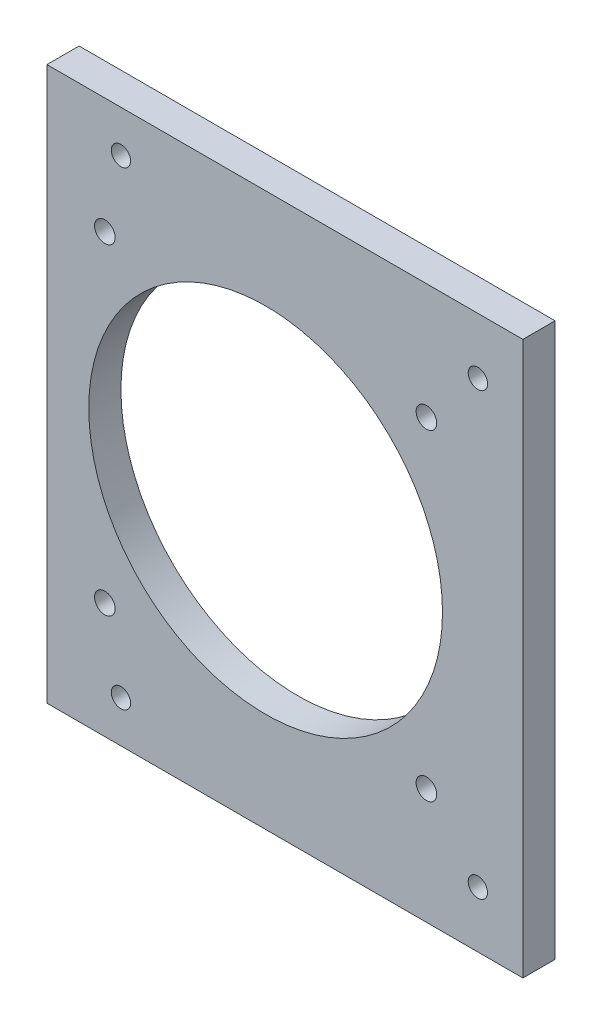
SolidWorks part; units mm, degrees
material "PBT Общее назначение"
ref_plane "Спереди" through (0, 0, 0) normal (0, 0, 1) x (1, 0, 0)
ref_plane "Сверху" through (0, 0, 0) normal (0, 1, 0) x (1, 0, 0)
ref_plane "Справа" through (0, 0, 0) normal (1, 0, 0) x (0, 0, -1)
sketch "Эскиз2" plane through (0, 0, 0) normal (0, 1, 0) x (1, 0, 0)
  line L0 (0, 0) -> (0, -131.0411) construction
  line L1 (0, 0) -> (-67.0136, 0) construction
sketch "Эскиз3" plane through (0, 0, 0) normal (0, 0, 1) x (1, 0, 0)
  line L0 (0, 0) -> (0, 105.2454) construction
sketch "Эскиз1" plane through (0, 0, 81) normal (0, 0, 1) x (1, 0, 0)
  line L0 (2.5, -5) -> (2.5, 95)
  line L1 (-67, -5) -> (-67, 95)
  line L2 (0, 0) -> (-67.0136, 0) construction
  line L3 (0, 0) -> (0, 105.2454) construction
  line L4 (-4.5, 79.25) -> (-4.5, 10.75) construction
  line L9 (2.5, 95) -> (-67, 95)
  line L11 (-67, -5) -> (2.5, -5)
  circle A1 centre (-60, 8.5) radius 1.5
  circle A6 centre (-60, 81.5) radius 1.5
  circle A8 centre (-4.5, 79.25) radius 1.5
  circle A10 centre (-4.5, 10.75) radius 1.5
  dimension "D5" = 7
  dimension "D6" = 7
  dimension "D3" = 3
  dimension "D4" = 13.5
  dimension "D7" = 15.75
  dimension "D8" = 15.75
  dimension "D9" = 7
  dimension "D10" = 13.5
  dimension "D2" = 100
  dimension "D1" = 69.5
  dimension "D11" = 5
  dimension "D12" = 2.5
extrude "Бобышка-Вытянуть1" add sketch "Эскиз1" against normal blind 5
sketch "Эскиз4" plane through (-67, 0, 0) normal (-1, 0, 0) x (0, 0, 1)
  line L0 (76, 95) -> (76, -5) construction
  line L1 (76, 95) -> (66, 95) construction
  line L2 (76, -5) -> (66, -5) construction
  line L3 (66, 95) -> (66, -5) construction
  dimension "D1" = 10
sketch "Эскиз5" plane through (0, 0, 81) normal (0, 0, 1) x (1, 0, 0)
  line L0 (-37.5, 73.2) -> (-37.5, 16.8) construction
  line L1 (-9.3, 45) -> (-65.7, 45) construction
  line L3 (-62.5, 70) -> (-12.5, 70) construction
  line L4 (-62.5, 70) -> (-62.5, 20) construction
  line L5 (-62.5, 20) -> (-12.5, 20) construction
  line L6 (-12.5, 70) -> (-12.5, 20) construction
  line L7 (-62.5, 70) -> (-12.5, 20) construction
  line L8 (-62.5, 20) -> (-12.5, 70) construction
  line L12 (-63.7, 26.06) -> (-61.07, 26.06)
  line L13 (-56.44, 21.43) -> (-56.44, 18.8)
  line L14 (-54.44, 16.8) -> (-20.56, 16.8)
  line L15 (-18.56, 18.8) -> (-18.56, 21.43)
  line L16 (-13.93, 26.06) -> (-11.3, 26.06)
  line L17 (-9.3, 28.06) -> (-9.3, 61.94)
  line L18 (-11.3, 63.94) -> (-13.93, 63.94)
  line L19 (-18.56, 68.57) -> (-18.56, 71.2)
  line L20 (-20.56, 73.2) -> (-54.44, 73.2)
  line L21 (-56.44, 71.2) -> (-56.44, 68.57)
  line L22 (-61.07, 63.94) -> (-63.7, 63.94)
  line L23 (-65.7, 61.94) -> (-65.7, 28.06)
  line L24 (-63.7, 26.06) -> (-61.07, 26.06) construction
  line L25 (-56.44, 21.43) -> (-56.44, 18.8) construction
  line L26 (-54.44, 16.8) -> (-20.56, 16.8) construction
  line L27 (-18.56, 18.8) -> (-18.56, 21.43) construction
  line L28 (-13.93, 26.06) -> (-11.3, 26.06) construction
  line L29 (-9.3, 28.06) -> (-9.3, 61.94) construction
  line L30 (-11.3, 63.94) -> (-13.93, 63.94) construction
  line L31 (-18.56, 68.57) -> (-18.56, 71.2) construction
  line L32 (-20.56, 73.2) -> (-54.44, 73.2) construction
  line L33 (-56.44, 71.2) -> (-56.44, 68.57) construction
  line L34 (-61.07, 63.94) -> (-63.7, 63.94) construction
  line L35 (-65.7, 61.94) -> (-65.7, 28.06) construction
  circle A0 centre (-12.5, 70) radius 1.6
  circle A1 centre (-12.5, 20) radius 1.6
  circle A2 centre (-62.5, 20) radius 1.6
  circle A3 centre (-62.5, 70) radius 1.6
  circle A4 centre (-37.5, 45) radius 27.5
  arc A12 (-65.7, 28.06) -> (-63.7, 26.06) centre (-63.7, 28.06) ccw
  arc A13 (-56.44, 21.43) -> (-61.07, 26.06) centre (-61.07, 21.43) ccw
  arc A14 (-56.44, 18.8) -> (-54.44, 16.8) centre (-54.44, 18.8) ccw
  arc A15 (-20.56, 16.8) -> (-18.56, 18.8) centre (-20.56, 18.8) ccw
  arc A16 (-13.93, 26.06) -> (-18.56, 21.43) centre (-13.93, 21.43) ccw
  arc A17 (-11.3, 26.06) -> (-9.3, 28.06) centre (-11.3, 28.06) ccw
  arc A18 (-9.3, 61.94) -> (-11.3, 63.94) centre (-11.3, 61.94) ccw
  arc A19 (-18.56, 68.57) -> (-13.93, 63.94) centre (-13.93, 68.57) ccw
  arc A20 (-18.56, 71.2) -> (-20.56, 73.2) centre (-20.56, 71.2) ccw
  arc A21 (-54.44, 73.2) -> (-56.44, 71.2) centre (-54.44, 71.2) ccw
  arc A22 (-61.07, 63.94) -> (-56.44, 68.57) centre (-61.07, 68.57) ccw
  arc A23 (-63.7, 63.94) -> (-65.7, 61.94) centre (-63.7, 61.94) ccw
  arc A24 (-65.7, 28.06) -> (-63.7, 26.06) centre (-63.7, 28.06) ccw construction
  arc A25 (-56.44, 21.43) -> (-61.07, 26.06) centre (-61.07, 21.43) ccw construction
  arc A26 (-56.44, 18.8) -> (-54.44, 16.8) centre (-54.44, 18.8) ccw construction
  arc A27 (-20.56, 16.8) -> (-18.56, 18.8) centre (-20.56, 18.8) ccw construction
  arc A28 (-13.93, 26.06) -> (-18.56, 21.43) centre (-13.93, 21.43) ccw construction
  arc A29 (-11.3, 26.06) -> (-9.3, 28.06) centre (-11.3, 28.06) ccw construction
  arc A30 (-9.3, 61.94) -> (-11.3, 63.94) centre (-11.3, 61.94) ccw construction
  arc A31 (-18.56, 68.57) -> (-13.93, 63.94) centre (-13.93, 68.57) ccw construction
  arc A32 (-18.56, 71.2) -> (-20.56, 73.2) centre (-20.56, 71.2) ccw construction
  arc A33 (-54.44, 73.2) -> (-56.44, 71.2) centre (-54.44, 71.2) ccw construction
  arc A34 (-61.07, 63.94) -> (-56.44, 68.57) centre (-61.07, 68.57) ccw construction
  arc A35 (-63.7, 63.94) -> (-65.7, 61.94) centre (-63.7, 61.94) ccw construction
  point P11 (-37.5, 45)
  dimension "D4" = 3.2
  dimension "D5" = 55
  dimension "D2" = 50
  dimension "D3" = 50
  dimension "D1" = 0
extrude "Вырез-Вытянуть1" cut sketch "Эскиз5" against normal through all
sketch "Эскиз6" plane through (-67, 0, 0) normal (-1, 0, 0) x (0, 0, 1)
  line L4 (81, -5) -> (81, 95)
  line L5 (81, 95) -> (76, 95)
  line L6 (76, 95) -> (76, -5)
  line L7 (76, -5) -> (81, -5)
  line L8 (81, -5) -> (81, 95)
  line L9 (81, 95) -> (76, 95)
  line L10 (76, 95) -> (76, -5)
  line L11 (76, -5) -> (81, -5)
  dimension "D1" = 0
extrude "Бобышка-Вытянуть2" add sketch "Эскиз6" along normal blind 4.5
sketch "Эскиз7" plane through (0, 95, 0) normal (0, 1, 0) x (1, 0, 0)
  line L4 (-71.5, -81) -> (2.5, -81)
  line L5 (2.5, -81) -> (2.5, -76)
  line L6 (2.5, -76) -> (-71.5, -76)
  line L7 (-71.5, -76) -> (-71.5, -81)
  line L8 (-71.5, -81) -> (2.5, -81)
  line L9 (2.5, -81) -> (2.5, -76)
  line L10 (2.5, -76) -> (-71.5, -76)
  line L11 (-71.5, -76) -> (-71.5, -81)
  dimension "D1" = 0
extrude "Вырез-Вытянуть2" cut sketch "Эскиз7" against normal blind 7
sketch "Эскиз8" plane through (0, -5, 0) normal (0, -1, 0) x (1, 0, 0)
  line L4 (2.5, 81) -> (-71.5, 81)
  line L5 (-71.5, 81) -> (-71.5, 76)
  line L6 (-71.5, 76) -> (2.5, 76)
  line L7 (2.5, 76) -> (2.5, 81)
  line L8 (2.5, 81) -> (-71.5, 81)
  line L9 (-71.5, 81) -> (-71.5, 76)
  line L10 (-71.5, 76) -> (2.5, 76)
  line L11 (2.5, 76) -> (2.5, 81)
  dimension "D1" = 0
extrude "Вырез-Вытянуть3" cut sketch "Эскиз8" against normal blind 7
